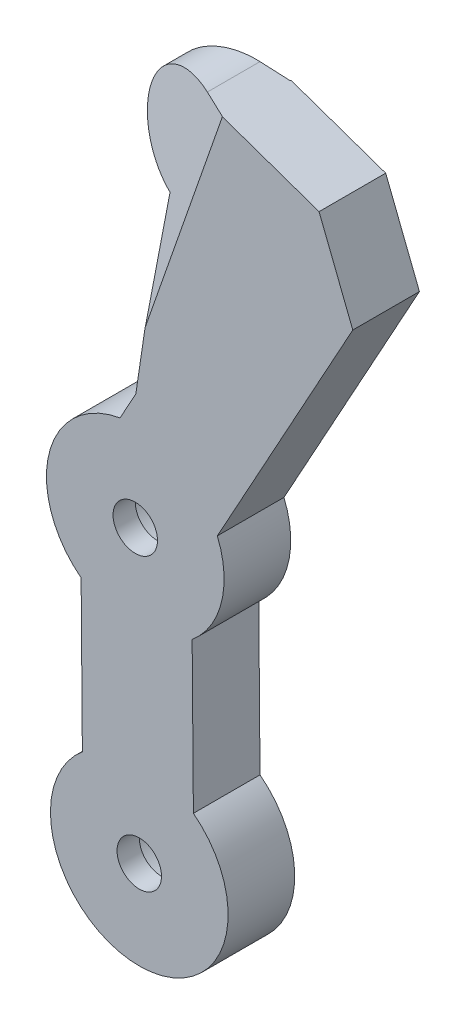
SolidWorks part; units mm, degrees
ref_plane "Front Plane" through (0, 0, 0) normal (0, 0, 1) x (1, 0, 0)
ref_plane "Top Plane" through (0, 0, 0) normal (0, 1, 0) x (1, 0, 0)
ref_plane "Right Plane" through (0, 0, 0) normal (1, 0, 0) x (0, 0, -1)
sketch "Sketch1" plane through (0, 0, 0) normal (0, 0, 1) x (1, 0, 0)
  line L0 (-0.8499, 17.4583) -> (0.0628, -47.5417) construction
  line L1 (5.5058, 85.326) -> (5.3078, 85.3936)
  line L2 (-13.0309, 1.6035) -> (-12.7512, -32.1859)
  line L3 (11.9643, 2.0941) -> (12.2436, -31.679)
  line L4 (17.6362, 25.116) -> (48.1292, 80.4952)
  line L5 (40.5387, 99.7888) -> (48.1292, 80.4952)
  line L6 (5.5058, 85.326) -> (-0.7156, 43.6177)
  line L8 (-0.8499, 17.4583) -> (38.1734, 87.2951) construction
  line L9 (-4.2703, 37.1618) -> (-0.7156, 43.6177)
  line L11 (38.1734, 87.2951) -> (9.8414, 97.1589) construction
  line L13 (40.5387, 99.7888) -> (13.9405, 109.0825)
  arc A0 (11.9643, 2.0941) -> (17.6362, 25.116) centre (-0.8397, 17.4583) ccw
  arc A4 (13.9405, 109.0825) -> (5.3078, 85.3936) centre (9.8414, 97.1589) ccw
  arc A6 (-4.2703, 37.1618) -> (-13.0309, 1.6035) centre (-0.8397, 17.4583) ccw
  arc A7 (-12.7512, -32.1859) -> (12.2436, -31.679) centre (0.0628, -47.5417) ccw
  point P2 (-0.3936, -25.0417)
  point P13 (18.4435, 32.4977)
  point P18 (23.5405, 72.3806)
  dimension "D5" = 30
  dimension "D6" = 80
  dimension "D7" = 65
  dimension "D11" = 40
  dimension "D12" = 40
  dimension "D1" = 0
  dimension "D2" = 210
  dimension "D3" = 0
  dimension "D4" = 80
  dimension "D13" = 0
  dimension "D14" = 0
extrude "Boss-Extrude1" add sketch "Sketch1" along normal blind 15
sketch "Sketch2" plane through (0, 0, 0) normal (0, 0, -1) x (-1, 0, 0)
  circle A0 centre (0.8397, 17.4583) radius 11.1
  arc A1 (13.0309, 1.6035) -> (4.2703, 37.1618) centre (0.8397, 17.4583) ccw construction
  circle A2 centre (-0.0628, -47.5417) radius 11.1
  arc A3 (-12.2436, -31.679) -> (12.7512, -32.1859) centre (-0.0628, -47.5417) ccw construction
  dimension "D1" = 0
  dimension "D2" = 0
  dimension "D3" = 22.2
  dimension "D4" = 22.2
extrude "Cut-Extrude1" cut sketch "Sketch2" against normal blind 10
sketch "Sketch3" plane through (0, 0, 10) normal (0, 0, -1) x (-1, 0, 0)
  circle A0 centre (0.8397, 17.4583) radius 5
  circle A1 centre (-0.0628, -47.5417) radius 5
  circle A2 centre (0.8397, 17.4583) radius 11.1 construction
  circle A3 centre (-0.0628, -47.5417) radius 11.1 construction
  dimension "D3" = 10
  dimension "D4" = 10
  dimension "D1" = 0
  dimension "D2" = 0
extrude "Cut-Extrude2" cut sketch "Sketch3" against normal blind 10
sketch "Sketch4" plane through (35.4845, 101.5548, 0) normal (0.3299, 0.944, 0) x (0.944, -0.3299, 0)
  line L0 (-17.1774, -0.156) -> (-35.8222, -5.2553)
  line L1 (-35.8586, -5.3691) -> (-36.0009, -9.9027)
  line L2 (-36.0009, -9.9027) -> (-17.6951, -14.9717)
extrude "Cut-Extrude-Thin7" cut sketch "Sketch4" against normal blind 62 thin
